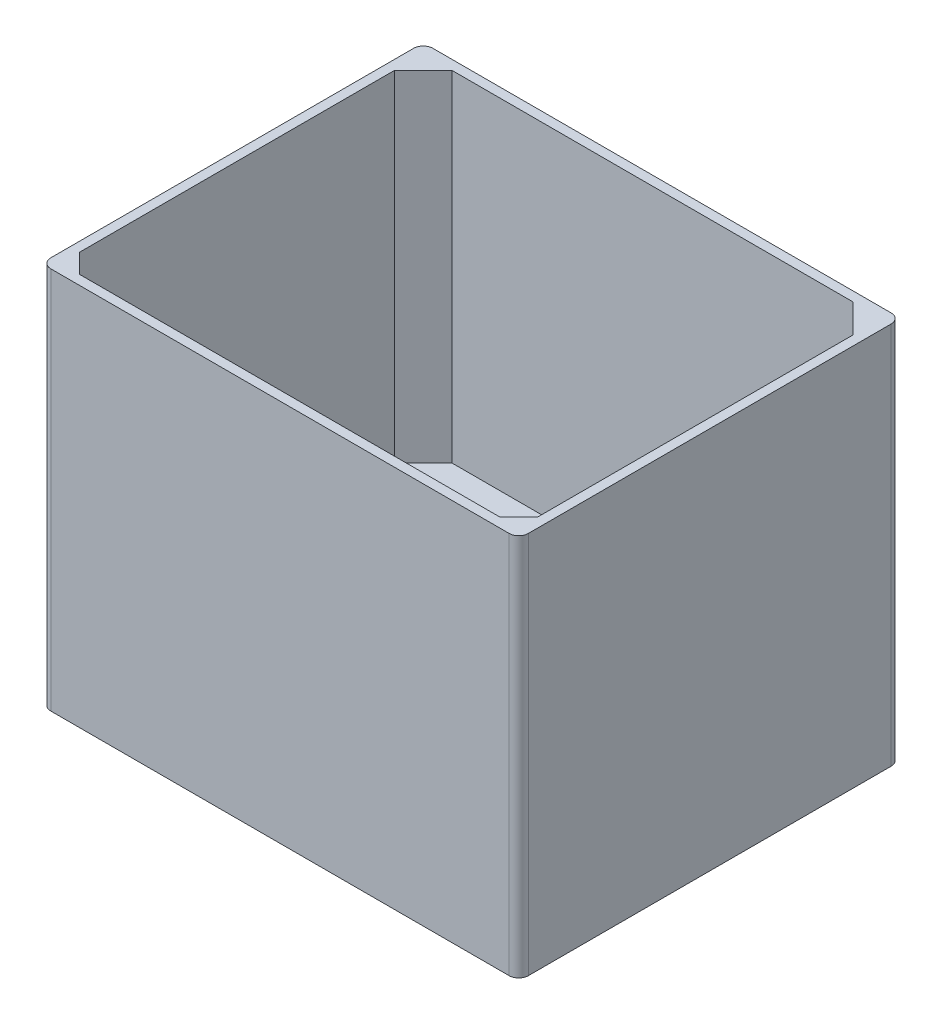
SolidWorks part; units mm, degrees
ref_plane "Front Plane" through (0, 0, 0) normal (0, 0, 1) x (1, 0, 0)
ref_plane "Top Plane" through (0, 0, 0) normal (0, 1, 0) x (1, 0, 0)
ref_plane "Right Plane" through (0, 0, 0) normal (1, 0, 0) x (0, 0, -1)
sketch "Sketch1" plane through (0, 0, 0) normal (0, 1, 0) x (1, 0, 0)
  line L1 (-40.9259, 33.4259) -> (59.0741, 33.4259)
  line L2 (-40.9259, 33.4259) -> (-40.9259, -46.5741)
  line L3 (-40.9259, -46.5741) -> (59.0741, -46.5741)
  line L4 (59.0741, 33.4259) -> (59.0741, -46.5741)
  dimension "D1" = 100
  dimension "D2" = 80
extrude "Boss-Extrude1" add sketch "Sketch1" along normal blind 80.2176
sketch "Sketch3" plane through (0, 80.2176, 0) normal (0, 1, 0) x (1, 0, 0)
  line L2 (9.0741, -1.1632) -> (46.8438, -1.1632)
  line L3 (46.8438, -1.1632) -> (46.8438, -42.7587)
  line L4 (46.8438, -42.7587) -> (9.0741, -42.7587)
  line L5 (9.0741, -42.7587) -> (-28.654, -42.7587)
  line L6 (-28.654, -42.7587) -> (-28.654, -1.1632)
  line L7 (-28.654, -1.1632) -> (9.0741, -1.1632)
shell "Shell1" thickness 2
extrude "Cut-Extrude2" cut sketch "Sketch3" against normal blind 180
fillet "Fillet3" radius 2 1 edges at (-40.9259, 40.1088, 46.5741)
fillet "Fillet4" radius 2 3 edges at (-40.9259, 40.1088, -33.4259) (59.0741, 40.1088, -33.4259) (59.0741, 40.1088, 46.5741)
chamfer "Chamfer2" distance 6 angle 45 1 edges at (-38.9259, 44.6088, -31.4259)
chamfer "Chamfer3" distance 6 angle 45 1 edges at (57.0741, 44.6088, -31.4259)
chamfer "Chamfer4" distance 4 angle 45 2 edges at (-38.9259, 44.6088, 44.5741) (57.0741, 44.6088, 44.5741)
sketch "Sketch4" plane through (0, 0, 0) normal (0, -1, 0) x (1, 0, 0)
  line L1 (-33.4167, 42.7649) -> (51.5833, 42.7649)
  line L2 (-33.4167, 42.7649) -> (-33.4167, -1.2351)
  line L3 (-33.4167, -1.2351) -> (51.5833, -1.2351)
  line L4 (51.5833, 42.7649) -> (51.5833, -1.2351)
  point P4 (49.0483, -1.3388)
  point P5 (50.7515, 42.7454)
  point P6 (37.297, 15.1905)
  point P7 (0, 0)
  point P8 (0, 0)
  point P9 (51.5833, 42.7649)
  dimension "D1" = 85
  dimension "D2" = 44
extrude "Cut-Extrude3" cut sketch "Sketch4" against normal blind 1
